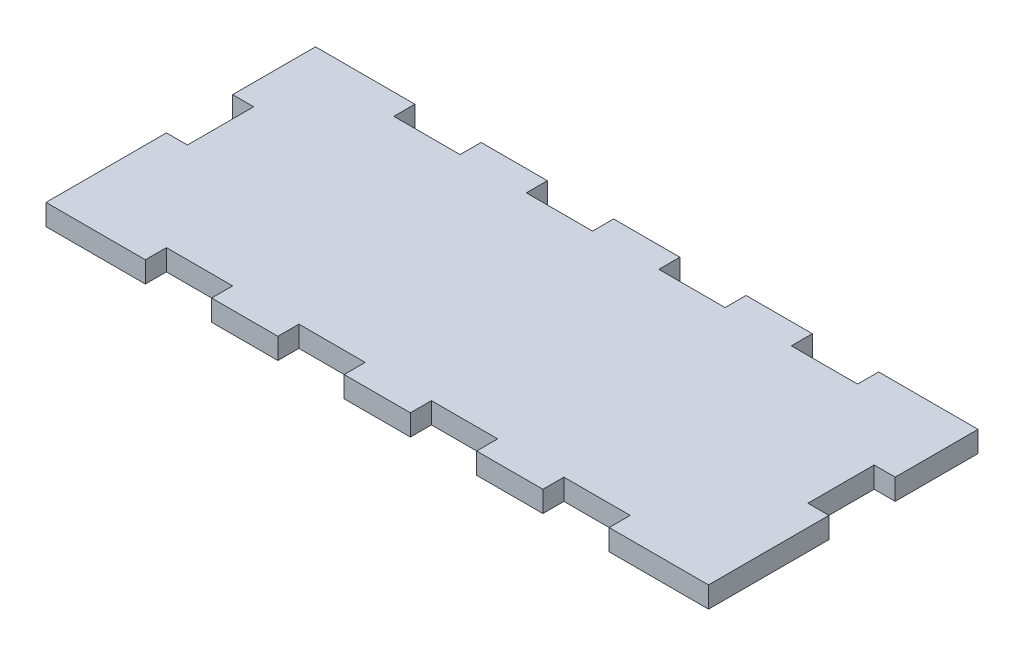
SolidWorks part; units mm, degrees
ref_plane "Front Plane" through (0, 0, 0) normal (0, 0, 1) x (1, 0, 0)
ref_plane "Top Plane" through (0, 0, 0) normal (0, 1, 0) x (1, 0, 0)
ref_plane "Right Plane" through (0, 0, 0) normal (1, 0, 0) x (0, 0, -1)
sketch "Sketch1" plane through (0, 0, 0) normal (0, 1, 0) x (1, 0, 0)
  line L0 (0, 37.5) -> (200, 37.5) construction
  line L1 (0, 0) -> (200, 0)
  line L2 (0, 0) -> (0, 75)
  line L3 (0, 75) -> (200, 75)
  line L4 (200, 0) -> (200, 75)
  line L5 (100, 75) -> (100, 0) construction
  line L6 (70, 0) -> (70, -6.35)
  line L7 (0, 0) -> (200, 0)
  line L8 (0, 0) -> (0, -6.35)
  line L9 (0, -6.35) -> (200, -6.35)
  line L10 (200, 0) -> (200, -6.35)
  line L11 (30, 0) -> (50, 0)
  line L12 (30, 0) -> (30, -6.35)
  line L13 (30, -6.35) -> (50, -6.35)
  line L14 (50, 0) -> (50, -6.35)
  line L15 (70, 0) -> (90, 0)
  line L16 (90, 0) -> (90, -6.35)
  line L17 (70, -6.35) -> (90, -6.35)
  line L18 (110, 0) -> (110, -6.35)
  line L19 (110, 0) -> (130, 0)
  line L20 (130, 0) -> (130, -6.35)
  line L21 (110, -6.35) -> (130, -6.35)
  line L22 (150, 0) -> (150, -6.35)
  line L23 (150, 0) -> (170, 0)
  line L24 (170, 0) -> (170, -6.35)
  line L25 (150, -6.35) -> (170, -6.35)
  line L26 (70, 75) -> (70, 68.65)
  line L27 (30, 75) -> (50, 75)
  line L28 (30, 75) -> (30, 68.65)
  line L29 (30, 68.65) -> (50, 68.65)
  line L30 (50, 75) -> (50, 68.65)
  line L31 (70, 75) -> (90, 75)
  line L32 (90, 75) -> (90, 68.65)
  line L33 (70, 68.65) -> (90, 68.65)
  line L34 (110, 75) -> (110, 68.65)
  line L35 (110, 75) -> (130, 75)
  line L36 (130, 75) -> (130, 68.65)
  line L37 (110, 68.65) -> (130, 68.65)
  line L38 (150, 75) -> (150, 68.65)
  line L39 (150, 75) -> (170, 75)
  line L40 (170, 75) -> (170, 68.65)
  line L41 (150, 68.65) -> (170, 68.65)
  line L42 (200, 30) -> (193.65, 30)
  line L43 (0, 50) -> (6.35, 50)
  line L44 (0, 50) -> (0, 30)
  line L45 (0, 30) -> (6.35, 30)
  line L46 (6.35, 50) -> (6.35, 30)
  line L47 (193.65, 50) -> (193.65, 30)
  line L48 (200, 50) -> (193.65, 50)
  line L49 (200, 50) -> (200, 30)
  dimension "D1" = 200
  dimension "D2" = 75
  dimension "D3" = 6.35
  dimension "D4" = 20
  dimension "D6" = 20
  dimension "D7" = 10
  dimension "D9" = 20
  dimension "D10" = 20
  dimension "D11" = 10
  dimension "D12" = 6.35
  dimension "D13" = 25
  dimension "D14" = 20
  dimension "D15" = 6.35
  dimension "D5" = 4
  dimension "D8" = 4
extrude "Boss-Extrude1" add sketch "Sketch1" along normal blind 6.35 contours L48 L4 L3 L40 L41 L38 L36 L37 L34 L32 L33 L26 L30 L29 L28 L2 L43 L46 L45 L1 L7 L42 L47 | L12 L1 L8 L9 | L1 L14 L9 L6 | L18 L7 L16 L9 | L22 L7 L20 L9 | L7 L24 L9 L10
